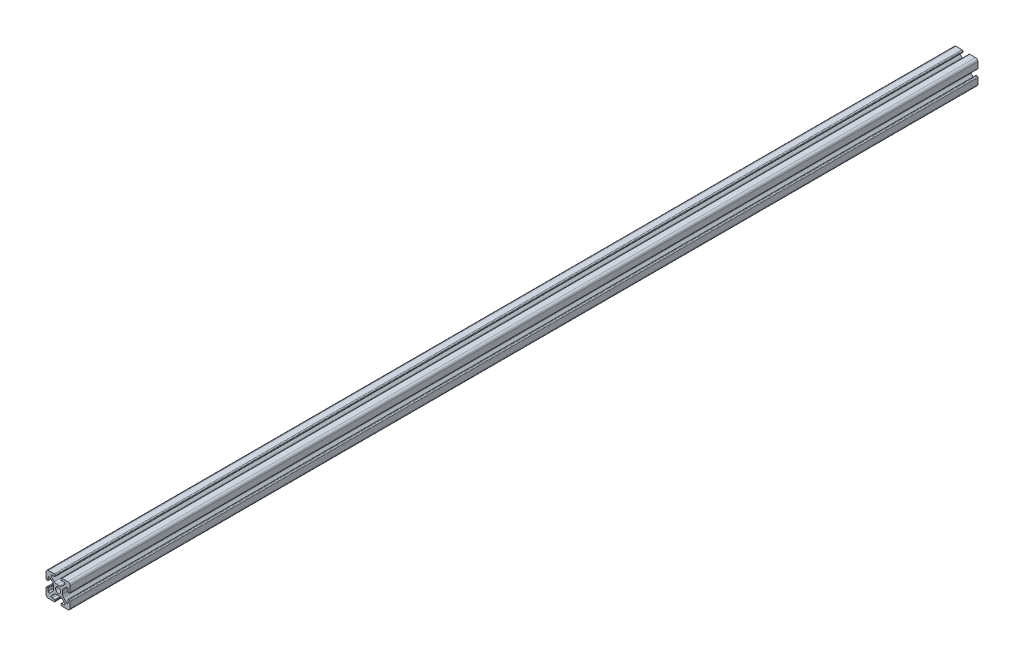
SolidWorks part; units mm, degrees
ref_plane "Front Plane" through (0, 0, 0) normal (0, 0, 1) x (1, 0, 0)
ref_plane "Top Plane" through (0, 0, 0) normal (0, 1, 0) x (1, 0, 0)
ref_plane "Right Plane" through (0, 0, 0) normal (1, 0, 0) x (0, 0, -1)
sketch "Sketch1" plane through (0, 0, 0) normal (0, 0, 1) x (1, 0, 0)
  line L0 (0, 10) -> (0, -10) construction
  line L1 (10, 0) -> (-10, 0) construction
  line L2 (-2.5, 10) -> (2.5, 10) construction
  line L3 (-5.75, 8.2) -> (5.75, 8.2) construction
  circle A0 centre (0, 0) radius 2.15 construction
  point P4 (0, 0)
  point P8 (0, 0)
  point P10 (0, 3.6)
  point P14 (0, 10)
  point P17 (0, 8.2)
  dimension "Thru Hole" = 4.3
  dimension "Height" = 20
  dimension "T Slot Depth" = 6.4
  dimension "T Slot Top Width" = 5
  dimension "T Slot Max Width" = 11.5
  dimension "Wall" = 1.8
sketch "Sketch2" plane through (0, 0, 0) normal (1, 0, 0) x (0, 0, -1)
  line L0 (375, 0) -> (-375, 0) construction
  point P4 (0, 0)
  dimension "D1" = 750
sketch "Sketch3" plane through (0, 0, 0) normal (0, 0, 1) x (1, 0, 0)
  line L0 (3.2874, 10) -> (8, 10)
  line L1 (10, 8) -> (10, -8) construction
  line L2 (8, -10) -> (-8, -10) construction
  line L3 (-10, 10) -> (10, -10) construction
  line L4 (2.5, 9.2126) -> (2.5, 8.5048)
  line L5 (-5.75, 8.2) -> (5.75, 8.2) construction
  line L6 (2.8048, 8.2) -> (4.9118, 8.2)
  line L7 (5.5045, 6.7691) -> (3.2141, 4.4787)
  line L8 (1.0928, 3.6) -> (-1.0928, 3.6)
  line L9 (0, 10) -> (0, -10) construction
  line L10 (5.75, 8.2) -> (5.75, 0) construction
  line L11 (10, 0) -> (-10, 0) construction
  line L12 (0, 0) -> (0, 10) construction
  line L13 (-2.5, 9.2126) -> (-2.5, 8.5048)
  line L14 (-5.5045, 6.7691) -> (-3.2141, 4.4787)
  line L15 (-2.8048, 8.2) -> (-4.9118, 8.2)
  line L16 (-3.2874, 10) -> (-8, 10)
  line L17 (0, 0) -> (-10, 0) construction
  line L18 (-10, 3.2874) -> (-10, 8)
  line L19 (-8.2, 2.8048) -> (-8.2, 4.9118)
  line L20 (-6.7691, 5.5045) -> (-4.4787, 3.2141)
  line L21 (-9.2126, 2.5) -> (-8.5048, 2.5)
  line L22 (-3.6, -1.0928) -> (-3.6, 1.0928)
  line L23 (-6.7691, -5.5045) -> (-4.4787, -3.2141)
  line L24 (-8.2, -2.8048) -> (-8.2, -4.9118)
  line L25 (-9.2126, -2.5) -> (-8.5048, -2.5)
  line L26 (-10, -3.2874) -> (-10, -8)
  line L27 (9.2126, -2.5) -> (8.5048, -2.5)
  line L28 (8.2, -2.8048) -> (8.2, -4.9118)
  line L29 (6.7691, -5.5045) -> (4.4787, -3.2141)
  line L30 (3.6, -1.0928) -> (3.6, 1.0928)
  line L31 (9.2126, 2.5) -> (8.5048, 2.5)
  line L32 (6.7691, 5.5045) -> (4.4787, 3.2141)
  line L33 (8.2, 2.8048) -> (8.2, 4.9118)
  line L34 (10, 8) -> (10, 3.2874)
  line L35 (10, -3.2874) -> (10, -8)
  line L36 (3.2874, -10) -> (8, -10)
  line L37 (-3.2874, -10) -> (-8, -10)
  line L38 (-6.7691, -5.5045) -> (-4.4787, -3.2141)
  line L39 (-2.8048, -8.2) -> (-4.9118, -8.2)
  line L40 (-5.5045, -6.7691) -> (-3.2141, -4.4787)
  line L41 (-2.5, -9.2126) -> (-2.5, -8.5048)
  line L42 (1.0928, -3.6) -> (-1.0928, -3.6)
  line L43 (5.5045, -6.7691) -> (3.2141, -4.4787)
  line L44 (2.8048, -8.2) -> (4.9118, -8.2)
  line L45 (2.5, -9.2126) -> (2.5, -8.5048)
  arc A0 (4.9118, 8.2) -> (5.5045, 6.7691) centre (4.9118, 7.3618) cw
  arc A1 (3.2141, 4.4787) -> (1.0928, 3.6) centre (1.0928, 6.6) cw
  circle A2 centre (0, 0) radius 2.15 construction
  circle A3 centre (0, 0) radius 2.15
  arc A4 (3.2874, 10) -> (2.5, 9.2126) centre (3.2874, 9.2126) ccw
  arc A5 (2.5, 8.5048) -> (2.8048, 8.2) centre (2.8048, 8.5048) ccw
  arc A6 (-3.2874, 10) -> (-2.5, 9.2126) centre (-3.2874, 9.2126) cw
  arc A7 (-4.9118, 8.2) -> (-5.5045, 6.7691) centre (-4.9118, 7.3618) ccw
  arc A8 (-3.2141, 4.4787) -> (-1.0928, 3.6) centre (-1.0928, 6.6) ccw
  arc A9 (-2.5, 8.5048) -> (-2.8048, 8.2) centre (-2.8048, 8.5048) cw
  arc A10 (-8.5048, 2.5) -> (-8.2, 2.8048) centre (-8.5048, 2.8048) ccw
  arc A11 (-4.4787, 3.2141) -> (-3.6, 1.0928) centre (-6.6, 1.0928) cw
  arc A12 (-8.2, 4.9118) -> (-6.7691, 5.5045) centre (-7.3618, 4.9118) cw
  arc A13 (-10, 3.2874) -> (-9.2126, 2.5) centre (-9.2126, 3.2874) ccw
  arc A14 (-8.5048, -2.5) -> (-8.2, -2.8048) centre (-8.5048, -2.8048) cw
  arc A15 (-10, -3.2874) -> (-9.2126, -2.5) centre (-9.2126, -3.2874) cw
  arc A16 (-4.4787, -3.2141) -> (-3.6, -1.0928) centre (-6.6, -1.0928) ccw
  arc A17 (-8.2, -4.9118) -> (-6.7691, -5.5045) centre (-7.3618, -4.9118) ccw
  arc A26 (-8, -10) -> (-10, -8) centre (-8, -8) cw
  arc A27 (-8, 10) -> (-10, 8) centre (-8, 8) ccw
  arc A28 (8, 10) -> (10, 8) centre (8, 8) cw
  arc A29 (10, -8) -> (8, -10) centre (8, -8) cw
  arc A30 (8.2, -4.9118) -> (6.7691, -5.5045) centre (7.3618, -4.9118) cw
  arc A31 (4.4787, -3.2141) -> (3.6, -1.0928) centre (6.6, -1.0928) cw
  arc A32 (10, -3.2874) -> (9.2126, -2.5) centre (9.2126, -3.2874) ccw
  arc A33 (8.5048, -2.5) -> (8.2, -2.8048) centre (8.5048, -2.8048) ccw
  arc A34 (10, 3.2874) -> (9.2126, 2.5) centre (9.2126, 3.2874) cw
  arc A35 (8.2, 4.9118) -> (6.7691, 5.5045) centre (7.3618, 4.9118) ccw
  arc A36 (4.4787, 3.2141) -> (3.6, 1.0928) centre (6.6, 1.0928) ccw
  arc A37 (8.5048, 2.5) -> (8.2, 2.8048) centre (8.5048, 2.8048) cw
  arc A38 (-2.5, -8.5048) -> (-2.8048, -8.2) centre (-2.8048, -8.5048) ccw
  arc A39 (-3.2141, -4.4787) -> (-1.0928, -3.6) centre (-1.0928, -6.6) cw
  arc A40 (-4.9118, -8.2) -> (-5.5045, -6.7691) centre (-4.9118, -7.3618) cw
  arc A41 (-3.2874, -10) -> (-2.5, -9.2126) centre (-3.2874, -9.2126) ccw
  arc A42 (2.5, -8.5048) -> (2.8048, -8.2) centre (2.8048, -8.5048) cw
  arc A43 (3.2874, -10) -> (2.5, -9.2126) centre (3.2874, -9.2126) cw
  arc A44 (3.2141, -4.4787) -> (1.0928, -3.6) centre (1.0928, -6.6) ccw
  arc A45 (4.9118, -8.2) -> (5.5045, -6.7691) centre (4.9118, -7.3618) ccw
  point P36 (2.5, 10)
  point P39 (2.5, 8.2)
  point P49 (0, 3.6)
  point P77 (-3.6, 0)
  point P78 (-8.2, -2.5)
  point P79 (-10, -2.5)
  point P104 (-10, -10)
  point P110 (10, 10)
  point P114 (10, -2.5)
  point P115 (8.2, -2.5)
  point P116 (3.6, 0)
  point P141 (0, -3.6)
  dimension "D1" = 3
  dimension "D2" = 0.8382
  dimension "D4" = 0.7874
  dimension "D5" = 0.3048
  dimension "D6" = 2
  dimension "D3" = 45
extrude "Boss-Extrude1" add sketch "Sketch3" along normal up to vertex (375 mm away) and the other way up to vertex (375 mm away) contours A45 L44 A42 L45 A43 L36 A29 L35 A32 L27 A33 L28 A30 L29 A31 L30 A36 L32 A35 L33 A37 L31 A34 L34 A28 L0 A4 L4 A5 L6 A0 L7 A1 L8 A8 L14 A7 L15 A9 L13 A6 L16 A27 L18 A13 L21 A10 L19 A12 L20 A11 up to point (0, 0, 375) other way up to point (0, 0, -375)
